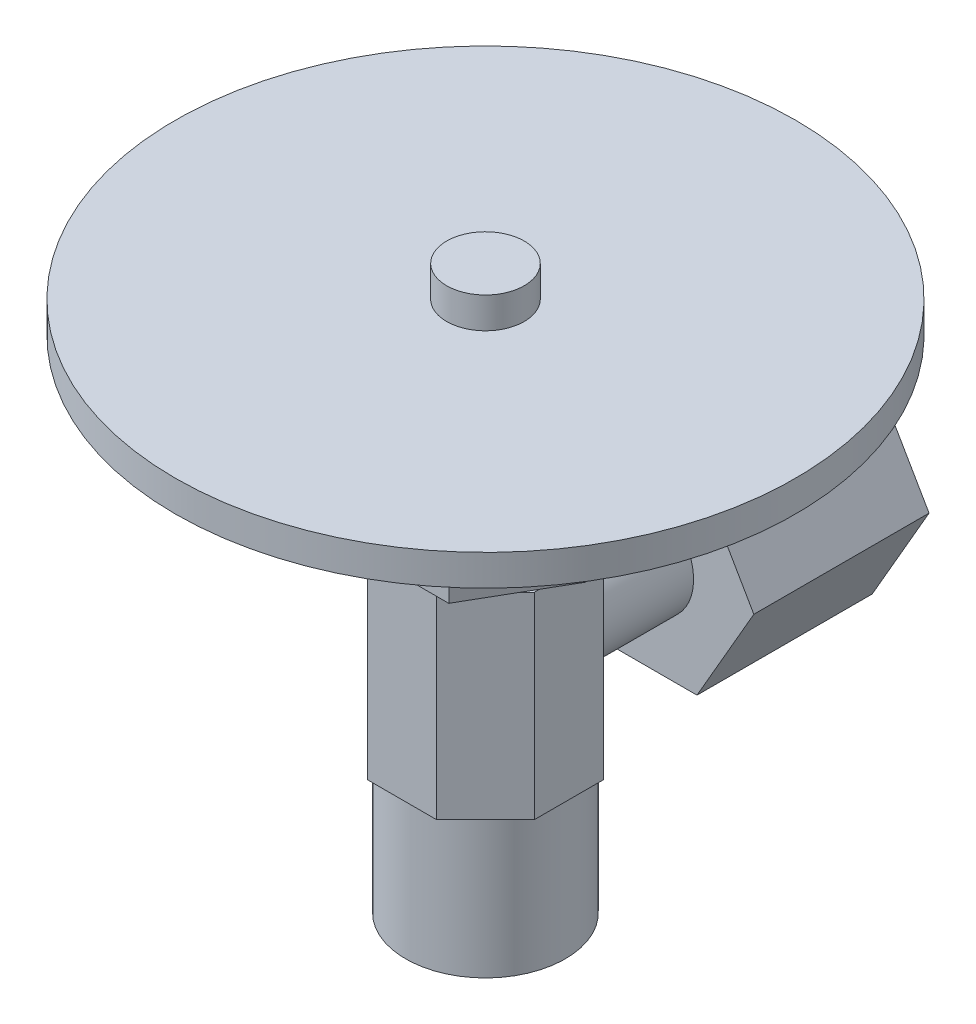
SolidWorks part; units mm, degrees
ref_plane "Front Plane" through (0, 0, 0) normal (0, 0, 1) x (1, 0, 0)
ref_plane "Top Plane" through (0, 0, 0) normal (0, 1, 0) x (1, 0, 0)
ref_plane "Right Plane" through (0, 0, 0) normal (1, 0, 0) x (0, 0, -1)
sketch "Sketch1" plane through (0, 0, 0) normal (0, 1, 0) x (1, 0, 0)
  line L0 (-2.2264, -5.375) -> (2.2264, -5.375)
  line L1 (5.375, -2.2264) -> (5.375, 2.2264)
  line L2 (5.375, 2.2264) -> (2.2264, 5.375)
  line L3 (2.2264, 5.375) -> (-2.2264, 5.375)
  line L4 (-2.2264, 5.375) -> (-5.375, 2.2264)
  line L5 (-5.375, 2.2264) -> (-5.375, -2.2264)
  line L6 (-5.375, -2.2264) -> (-2.2264, -5.375)
  line L7 (2.2264, -5.375) -> (5.375, -2.2264)
  circle A0 centre (0, 0) radius 5.375 construction
  dimension "D1" = 10.75
extrude "Boss-Extrude1" add sketch "Sketch1" along normal blind 12.7
sketch "Sketch2" plane through (0, 0, -5.375) normal (0, 0, -1) x (-1, 0, 0)
  line L0 (-2.2264, 12.7) -> (2.2264, 0) construction
  line L1 (2.2264, 0) -> (5.375, 0) construction
  line L2 (2.2264, 12.7) -> (2.2264, 0) construction
  circle A0 centre (0, 6.35) radius 3.445
extrude "Boss-Extrude2" add sketch "Sketch2" along normal blind 4.6 and the other way blind 2
sketch "Sketch3" plane through (0, 0, -9.975) normal (0, 0, -1) x (-1, 0, 0)
  line L1 (7.3323, 6.35) -> (3.6662, 12.7)
  line L2 (3.6662, 12.7) -> (-3.6662, 12.7)
  line L3 (-3.6662, 12.7) -> (-7.3323, 6.35)
  line L4 (-7.3323, 6.35) -> (-3.6662, 0)
  line L5 (-3.6662, 0) -> (3.6662, 0)
  line L6 (3.6662, 0) -> (7.3323, 6.35)
  circle A0 centre (0, 6.35) radius 6.35 construction
  dimension "D1" = 12.7
extrude "Boss-Extrude3" add sketch "Sketch3" along normal blind 11.3
sketch "Sketch4" plane through (0, 0, 0) normal (0, -1, 0) x (1, 0, 0)
  circle A0 centre (0, 0) radius 5.15
  dimension "D1" = 10.3
extrude "Boss-Extrude4" add sketch "Sketch4" along normal blind 9
sketch "Sketch5" plane through (0, 12.7, 0) normal (0, 1, 0) x (1, 0, 0)
  line L1 (6.4663, 0) -> (3.2332, 5.6)
  line L2 (3.2332, 5.6) -> (-3.2332, 5.6)
  line L3 (-3.2332, 5.6) -> (-6.4663, 0)
  line L4 (-6.4663, 0) -> (-3.2332, -5.6)
  line L5 (-3.2332, -5.6) -> (3.2332, -5.6)
  line L6 (3.2332, -5.6) -> (6.4663, 0)
  circle A0 centre (0, 0) radius 5.6 construction
  dimension "D1" = 11.2
extrude "Boss-Extrude5" add sketch "Sketch5" along normal blind 8.57
sketch "Sketch6" plane through (0, 21.27, 0) normal (0, 1, 0) x (1, 0, 0)
  circle A0 centre (0, 0) radius 2.5
  dimension "D1" = 5
extrude "Boss-Extrude6" add sketch "Sketch6" along normal blind 6
sketch "Sketch7" plane through (0, 27.27, 0) normal (0, 1, 0) x (1, 0, 0)
  circle A0 centre (0, 0) radius 20
  dimension "D1" = 40
extrude "Boss-Extrude7" add sketch "Sketch7" against normal blind 2 from offset 2
